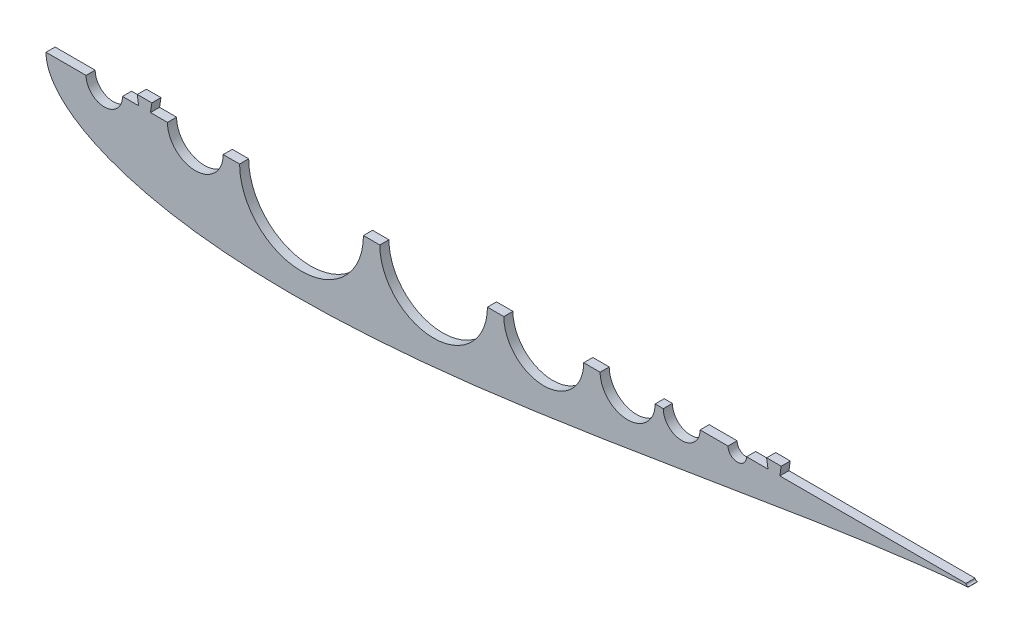
SolidWorks part; units mm, degrees
ref_plane "Front Plane" through (0, 0, 0) normal (0, 0, 1) x (1, 0, 0)
ref_plane "Top Plane" through (0, 0, 0) normal (0, 1, 0) x (1, 0, 0)
ref_plane "Right Plane" through (0, 0, 0) normal (1, 0, 0) x (0, 0, -1)
curve "Curve4"
  spline degree 3 poles (100, 0, 0) (99.8498, 0.0023, 0) (99.4759, 0.008, 0) (99.1023, 0.0238, 0) (98.8789, 0.0332, 0) knots 0 0 0 0 0.401829 1 1 1 1
curve "Curve5"
  spline degree 3 poles (99.3714, -0.0082, 0) (100.2526, 0, 0) (99.3714, 0.0082, 0) (98.8504, 0.035, 0) (97.904, 0.0811, 0) (96.8285, 0.1543, 0) (95.5159, 0.2583, 0) (94.013, 0.3972, 0) (92.313, 0.574, 0) (90.4281, 0.791, 0) (88.3655, 1.0495, 0) (86.1348, 1.3497, 0) (83.7456, 1.691, 0) (81.2082, 2.0715, 0) (78.5335, 2.4886, 0) (75.7326, 2.9386, 0) (72.8172, 3.4168, 0) (69.799, 3.9177, 0) (66.6904, 4.435, 0) (63.5039, 4.9616, 0) (60.2521, 5.4899, 0) (56.948, 6.0119, 0) (53.6049, 6.519, 0) (50.2363, 7.0024, 0) (46.8558, 7.4534, 0) (43.4774, 7.8632, 0) (40.1152, 8.2232, 0) (36.7837, 8.5249, 0) (33.4975, 8.7606, 0) (30.2716, 8.923, 0) (27.1211, 9.0055, 0) (24.0614, 9.0025, 0) (21.108, 8.909, 0) (18.277, 8.7213, 0) (15.5843, 8.4369, 0) (13.0466, 8.0543, 0) (10.6806, 7.5735, 0) (8.5039, 6.996, 0) (6.5349, 6.3253, 0) (4.7933, 5.5673, 0) (3.3001, 4.7321, 0) (2.0777, 3.8366, 0) (1.1467, 2.91, 0) (0.5165, 2.0014, 0) (0.165, 1.1816, 0) (0.0231, 0.524, 0) (-0.0093, 0, 0) (0.0231, -0.524, 0) (0.165, -1.1816, 0) (0.5165, -2.0014, 0) (1.1467, -2.91, 0) (2.0777, -3.8366, 0) (3.3001, -4.7321, 0) (4.7933, -5.5673, 0) (6.5349, -6.3253, 0) (8.5039, -6.996, 0) (10.6806, -7.5735, 0) (13.0466, -8.0543, 0) (15.5843, -8.4369, 0) (18.277, -8.7213, 0) (21.108, -8.909, 0) (24.0614, -9.0025, 0) (27.1211, -9.0055, 0) (30.2716, -8.923, 0) (33.4975, -8.7606, 0) (36.7837, -8.5249, 0) (40.1152, -8.2232, 0) (43.4774, -7.8632, 0) (46.8558, -7.4534, 0) (50.2363, -7.0024, 0) (53.6049, -6.519, 0) (56.948, -6.0119, 0) (60.2521, -5.4899, 0) (63.5039, -4.9616, 0) (66.6904, -4.435, 0) (69.799, -3.9177, 0) (72.8172, -3.4168, 0) (75.7326, -2.9386, 0) (78.5335, -2.4886, 0) (81.2082, -2.0715, 0) (83.7456, -1.691, 0) (86.1348, -1.3497, 0) (88.3655, -1.0495, 0) (90.4281, -0.791, 0) (92.313, -0.574, 0) (94.013, -0.3972, 0) (95.5159, -0.2583, 0) (96.8285, -0.1543, 0) (97.904, -0.0811, 0) (98.8504, -0.035, 0) (99.3714, -0.0082, 0) (100.2526, 0, 0) (99.3714, 0.0082, 0) knots -0.009667 -0.005395 -0.002168 0 0.002168 0.005395 0.009667 0.014967 0.021271 0.028553 0.036781 0.04592 0.055932 0.066773 0.078397 0.090755 0.103793 0.117456 0.131686 0.146422 0.1616 0.177156 0.193024 0.209135 0.225421 0.241812 0.258238 0.274629 0.290914 0.307025 0.322893 0.338448 0.353626 0.368361 0.38259 0.396253 0.40929 0.421647 0.43327 0.444109 0.454119 0.463255 0.471479 0.478755 0.485052 0.490344 0.49461 0.497833 0.5 0.502167 0.50539 0.509656 0.514948 0.521245 0.528521 0.536745 0.545881 0.555891 0.56673 0.578353 0.59071 0.603747 0.61741 0.631639 0.646374 0.661552 0.677107 0.692975 0.709086 0.725371 0.741762 0.758188 0.774579 0.790865 0.806976 0.822844 0.8384 0.853578 0.868314 0.882544 0.896207 0.909245 0.921603 0.933227 0.944068 0.95408 0.963219 0.971447 0.978729 0.985033 0.990333 0.994605 0.997832 1 1.002168 1.005395 1.009667 periodic
sketch "Sketch2" plane through (0, 0, 0) normal (0, 0, 1) x (1, 0, 0)
  line L0 (100, 0) -> (0, 0) construction
  line L1 (1.2169, -991.9959) -> (1.2169, 49008.0041) construction
  line L2 (84.709, 0) -> (123.571, 0) construction
  line L3 (125.634, 0) -> (131.6629, 0) construction
  line L4 (643.5991, 0) -> (643.5991, -1.016)
  line L9 (0, 0) -> (643.9668, 0)
  line L13 (460.661, 0) -> (473.361, 0)
  circle A0 centre (104.14, 0) radius 19.431 construction
  arc A1 (1.2169, -4.6585) -> (1.2169, 4.6585) centre (9.525, 0) cw
  arc A2 (641.5671, 0) -> (644.1071, 0) centre (642.8371, 0) ccw
  circle A4 centre (104.14, 0) radius 19.431
  circle A9 centre (40.64, 0) radius 12.7
  circle A14 centre (642.3793, 0) radius 1.5875 construction
  arc A15 (642.5108, -1.582) -> (642.5108, 1.582) centre (642.3793, 0) ccw
  spline S2 degree 3 poles (666.3448, -0.0547) (672.2538, 0) (666.3448, 0.0547) (662.8509, 0.2344) (656.505, 0.5436) (649.293, 1.0348) (640.4916, 1.7319) (630.4138, 2.6634) (619.0141, 3.8493) (606.375, 5.3044) (592.5439, 7.0376) (577.5855, 9.0506) (561.5643, 11.3389) (544.5497, 13.8907) (526.6141, 16.6877) (507.8326, 19.7051) (488.2827, 22.9117) (468.0444, 26.2704) (447.1994, 29.739) (425.8316, 33.2703) (404.0263, 36.8132) (381.8707, 40.3133) (359.4533, 43.7135) (336.8645, 46.9554) (314.1962, 49.9798) (291.5418, 52.7277) (268.9963, 55.1412) (246.6566, 57.1646) (224.6209, 58.7452) (202.9892, 59.8341) (181.8631, 60.3875) (161.3458, 60.367) (141.542, 59.7399) (122.5581, 58.4818) (104.5023, 56.5743) (87.485, 54.0089) (71.6197, 50.7848) (57.0237, 46.9125) (43.8205, 42.415) (32.1416, 37.3322) (22.1291, 31.7315) (13.9324, 25.7264) (7.6896, 19.5132) (3.4631, 13.4204) (1.1063, 7.9234) (0.1546, 3.5138) (-0.0622, 0) (0.1546, -3.5138) (1.1063, -7.9234) (3.4631, -13.4204) (7.6896, -19.5132) (13.9324, -25.7264) (22.1291, -31.7315) (32.1416, -37.3322) (43.8205, -42.415) (57.0237, -46.9125) (71.6197, -50.7848) (87.485, -54.0089) (104.5023, -56.5743) (122.5581, -58.4818) (141.542, -59.7399) (161.3458, -60.367) (181.8631, -60.3875) (202.9892, -59.8341) (224.6209, -58.7452) (246.6566, -57.1646) (268.9963, -55.1412) (291.5418, -52.7277) (314.1962, -49.9798) (336.8645, -46.9554) (359.4533, -43.7135) (381.8707, -40.3133) (404.0263, -36.8132) (425.8316, -33.2703) (447.1994, -29.739) (468.0444, -26.2704) (488.2827, -22.9117) (507.8326, -19.7051) (526.6141, -16.6877) (544.5497, -13.8907) (561.5643, -11.3389) (577.5855, -9.0506) (592.5439, -7.0376) (606.375, -5.3044) (619.0141, -3.8493) (630.4138, -2.6634) (640.4916, -1.7319) (649.293, -1.0348) (656.505, -0.5436) (662.8509, -0.2344) (666.3448, -0.0547) (672.2538, 0) (666.3448, 0.0547) knots -0.009667 -0.005395 -0.002168 0 0.002168 0.005395 0.009667 0.014967 0.021271 0.028553 0.036781 0.04592 0.055932 0.066773 0.078397 0.090755 0.103793 0.117456 0.131686 0.146422 0.1616 0.177156 0.193024 0.209135 0.225421 0.241812 0.258238 0.274629 0.290914 0.307025 0.322893 0.338448 0.353626 0.368361 0.38259 0.396253 0.40929 0.421647 0.43327 0.444109 0.454119 0.463255 0.471479 0.478755 0.485052 0.490344 0.49461 0.497833 0.5 0.502167 0.50539 0.509656 0.514948 0.521245 0.528521 0.536745 0.545881 0.555891 0.56673 0.578353 0.59071 0.603747 0.61741 0.631639 0.646374 0.661552 0.677107 0.692975 0.709086 0.725371 0.741762 0.758188 0.774579 0.790865 0.806976 0.822844 0.8384 0.853578 0.868314 0.882544 0.896207 0.909245 0.921603 0.933227 0.944068 0.95408 0.963219 0.971447 0.978729 0.985033 0.990333 0.994605 0.997832 1 1.002168 1.005395 1.009667 only from (670.56, 0) to (670.56, 0)
  point P2 (167.64, 0)
  point P8 (1.2169, -4.6585)
  point P10 (1.2169, 4.6585)
  point P25 (0, 0)
  point P26 (644.0685, 0)
  point P27 (642.873, 0)
  point P28 (133.9182, 0)
  point P29 (0, 0)
  point P49 (130.0977, 0)
  point P59 (95.1064, 0)
  dimension "D2" = 38.862
  dimension "D3" = 1.016
  dimension "D4" = 1.27
  dimension "D8" = 25.4
  dimension "D9" = 63.5
  dimension "D10" = 3.175
  dimension "D1" = 167.64
  dimension "D6" = 63.5
extrude "Boss-Extrude1" add sketch "Sketch2" along normal blind 6.35
sketch "Sketch3" plane through (0, 0, 6.35) normal (0, 0, 1) x (1, 0, 0)
  line L0 (84.14, -12.7) -> (62.637, -12.7) construction
  line L1 (430.4749, -1041.2705) -> (430.4749, 48958.7295) construction
  line L2 (123.571, 0) -> (641.5671, 0) construction
  line L3 (27.94, 0) -> (0, 0)
  line L4 (641.5671, 0) -> (123.571, 0)
  line L5 (84.709, 0) -> (53.34, 0)
  line L6 (27.94, 0) -> (0, 0)
  line L7 (221.3683, -1000) -> (221.3683, 49000) construction
  line L8 (84.709, 0) -> (53.34, 0)
  line L9 (232.7983, -1000) -> (232.7983, 49000) construction
  line L10 (307.8396, -1000) -> (307.8396, 49000) construction
  line L11 (319.2696, -1000) -> (319.2696, 49000) construction
  line L12 (374.9948, -1000) -> (374.9948, 49000) construction
  line L13 (84.709, -17.145) -> (65.0689, -17.145) construction
  line L14 (424.7788, -1000) -> (424.7788, 49000) construction
  line L15 (135.001, -1000) -> (135.001, 49000) construction
  line L16 (386.4248, -1000) -> (386.4248, 49000) construction
  line L17 (52.7726, -27.2676) -> (52.7726, -27.2676) construction
  arc A0 (36.4352, -25.0495) -> (62.637, -12.7) centre (40.64, 0) ccw construction
  circle A2 centre (178.1847, 0) radius 43.1837
  arc A3 (642.5108, -1.582) -> (643.5991, -1.016) centre (642.3793, 0) ccw
  arc A4 (84.709, 0) -> (123.571, 0) centre (104.14, 0) ccw
  arc A5 (27.94, 0) -> (53.34, 0) centre (40.64, 0) ccw
  arc A6 (642.5108, -1.582) -> (643.5991, -1.016) centre (642.3793, 0) ccw
  circle A7 centre (270.319, 0) radius 37.5206
  arc A8 (27.94, 0) -> (53.34, 0) centre (40.64, 0) ccw
  circle A9 centre (347.1322, 0) radius 27.8626
  circle A10 centre (405.6018, 0) radius 19.177
  circle A11 centre (443.3019, 0) radius 12.827
  circle A12 centre (482.0825, 0) radius 6.477
  arc A13 (52.7726, -27.2676) -> (65.0689, -17.145) centre (40.64, 0) ccw construction
  arc A14 (638.2053, 15.2585) -> (638.2053, 15.2585) centre (638.2053, 15.2585) ccw construction
  arc A18 (641.5671, 0) -> (643.5991, -1.016) centre (642.8371, 0) ccw
  arc A19 (641.5671, 0) -> (643.5991, -1.016) centre (642.8371, 0) ccw
  spline S1 degree 3 poles (1083.539, -1665.6175) (237.9838, 156.2926) (-13.4194, 59.3783) (1.1063, -7.9234) (3.4631, -13.4204) (7.6896, -19.5132) (13.9324, -25.7264) (22.1291, -31.7315) (32.1416, -37.3322) (43.8205, -42.415) (57.0237, -46.9125) (71.6197, -50.7848) (87.485, -54.0089) (104.5023, -56.5743) (122.5581, -58.4818) (141.542, -59.7399) (161.3458, -60.367) (181.8631, -60.3875) (202.9892, -59.8341) (224.6209, -58.7452) (246.6566, -57.1646) (268.9963, -55.1412) (291.5418, -52.7277) (314.1962, -49.9798) (336.8645, -46.9554) (359.4533, -43.7135) (381.8707, -40.3133) (404.0263, -36.8132) (425.8316, -33.2703) (447.1994, -29.739) (468.0444, -26.2704) (488.2827, -22.9117) (507.8326, -19.7051) (526.6141, -16.6877) (544.5497, -13.8907) (561.5643, -11.3389) (577.5855, -9.0506) (592.5439, -7.0376) (606.375, -5.3044) (619.0141, -3.8493) (630.4138, -2.6634) (741.1247, 7.5694) (864.0226, -5.3554) (-1347.5502, -198.2161) knots 0.362281 0.362281 0.362281 0.362281 0.502167 0.50539 0.509656 0.514948 0.521245 0.528521 0.536745 0.545881 0.555891 0.56673 0.578353 0.59071 0.603747 0.61741 0.631639 0.646374 0.661552 0.677107 0.692975 0.709086 0.725371 0.741762 0.758188 0.774579 0.790865 0.806976 0.822844 0.8384 0.853578 0.868314 0.882544 0.896207 0.909245 0.921603 0.933227 0.944068 0.95408 0.963219 0.971447 0.978729 1.20286 1.20286 1.20286 1.20286 only from (0, 0) to (642.5108, -1.582)
  spline S2 degree 3 poles (0, 0) (0, -1.0075) (0.1546, -3.5138) (1.1063, -7.9234) (3.4631, -13.4204) (7.6896, -19.5132) (13.9324, -25.7264) (22.1291, -31.7315) (32.1416, -37.3322) (43.8205, -42.415) (57.0237, -46.9125) (71.6197, -50.7848) (87.485, -54.0089) (104.5023, -56.5743) (122.5581, -58.4818) (141.542, -59.7399) (161.3458, -60.367) (181.8631, -60.3875) (202.9892, -59.8341) (224.6209, -58.7452) (246.6566, -57.1646) (268.9963, -55.1412) (291.5418, -52.7277) (314.1962, -49.9798) (336.8645, -46.9554) (359.4533, -43.7135) (381.8707, -40.3133) (404.0263, -36.8132) (425.8316, -33.2703) (447.1994, -29.739) (468.0444, -26.2704) (488.2827, -22.9117) (507.8326, -19.7051) (526.6141, -16.6877) (544.5497, -13.8907) (561.5643, -11.3389) (577.5855, -9.0506) (592.5439, -7.0376) (606.375, -5.3044) (619.0141, -3.8493) (630.4138, -2.6634) (638.0937, -1.9535) (641.9934, -1.6251) (642.5108, -1.582) knots 0.5 0.5 0.5 0.5 0.502167 0.50539 0.509656 0.514948 0.521245 0.528521 0.536745 0.545881 0.555891 0.56673 0.578353 0.59071 0.603747 0.61741 0.631639 0.646374 0.661552 0.677107 0.692975 0.709086 0.725371 0.741762 0.758188 0.774579 0.790865 0.806976 0.822844 0.8384 0.853578 0.868314 0.882544 0.896207 0.909245 0.921603 0.933227 0.944068 0.95408 0.963219 0.971447 0.978729 0.979843 0.979843 0.979843 0.979843
  spline S4 degree 1 poles (52.7726, -27.2676) (638.2053, 15.2585) knots 0 0 1 1 construction
  spline S5 degree 3 poles (52.7726, -27.2676) (54.098, -27.7509) (56.7529, -28.6784) (62.1794, -30.4243) (69.1006, -32.3953) (77.5892, -34.4571) (89.0862, -36.8389) (103.7331, -39.1926) (127.5352, -41.8455) (149.5112, -42.9751) (171.6139, -43.2629) (184.6425, -43.1469) (205.1644, -42.6052) (230.9293, -41.2613) (259.7939, -38.828) (285.4834, -36.1555) (308.0659, -33.4851) (336.7822, -29.6913) (372.3922, -24.4911) (406.8647, -19.0063) (435.2357, -14.3425) (451.6826, -11.6119) (464.2574, -9.5208) (476.8398, -7.4307) (497.3171, -4.0443) (526.9629, 0.7645) (562.929, 6.2684) (594.1055, 10.5252) (616.0859, 13.0867) (628.694, 14.3901) (635.0364, 14.9826) (638.2053, 15.2585) knots 0.548481 0.548481 0.548481 0.548481 0.551835 0.555189 0.561898 0.568606 0.575315 0.588731 0.602148 0.628982 0.637543 0.65096 0.657668 0.682649 0.707463 0.72088 0.738887 0.756894 0.783728 0.816817 0.832298 0.845715 0.852722 0.859728 0.873145 0.897318 0.924152 0.950985 0.964402 0.971111 0.977819 0.977819 0.977819 0.977819 construction
  line M19 (641.5671, 0) -> (123.571, 0)
  dimension "D3" = 11.43
  dimension "D7" = 38.354
  dimension "D8" = 25.654
  dimension "D9" = 12.954
  dimension "D4" = 11.43
  dimension "D5" = 11.43
  dimension "D6" = 11.43
  dimension "D1" = 0
  dimension "D10" = 17.145
extrude "Cut-Extrude2" cut sketch "Sketch3" against normal through all both and the other way through all contours A2 M19 | A7 M19 | A9 M19 | A10 M19 | A11 M19 | A12 M19
sketch "Sketch4" plane through (0, 0, 6.35) normal (0, 0, 1) x (1, 0, 0)
  line L0 (63.66, 6.35) -> (73.82, 6.35)
  line L1 (65.565, 6.35) -> (71.915, 6.35)
  line L2 (65.565, 6.35) -> (65.565, -6.35)
  line L3 (65.565, -6.35) -> (71.915, -6.35)
  line L4 (71.915, 6.35) -> (71.915, -6.35)
  line L5 (65.565, 6.35) -> (71.915, -6.35) construction
  line L6 (65.565, -6.35) -> (71.915, 6.35) construction
  line L7 (71.915, -6.35) -> (73.82, 6.35)
  line L8 (63.66, 6.35) -> (65.565, -6.35)
  line L9 (232.7983, 0) -> (221.3683, 0)
  line L18 (232.7983, 0) -> (221.3683, 0)
  line L20 (135.001, 0) -> (123.571, 0)
  line L21 (135.001, 0) -> (123.571, 0)
  line L22 (84.709, 0) -> (53.34, 0)
  line L23 (84.709, 0) -> (53.34, 0)
  line L24 (27.94, 0) -> (0, 0)
  line L25 (27.94, 0) -> (0, 0)
  line L26 (641.5671, 0) -> (488.5595, 0)
  line L27 (502.5295, 6.35) -> (512.6895, 6.35)
  line L28 (504.4345, 6.35) -> (510.7845, 6.35)
  line L29 (504.4345, 6.35) -> (504.4345, -6.35)
  line L30 (504.4345, -6.35) -> (510.7845, -6.35)
  line L31 (510.7845, 6.35) -> (510.7845, -6.35)
  line L32 (504.4345, 6.35) -> (510.7845, -6.35) construction
  line L33 (504.4345, -6.35) -> (510.7845, 6.35) construction
  line L34 (504.4345, -6.35) -> (502.5295, 6.35)
  line L35 (510.7845, -6.35) -> (512.6895, 6.35)
  line L36 (641.5671, 0) -> (488.5595, 0)
  line L37 (475.6055, 0) -> (456.1289, 0)
  line L38 (475.6055, 0) -> (456.1289, 0)
  line L39 (430.4749, 0) -> (424.7788, 0)
  line L40 (430.4749, 0) -> (424.7788, 0)
  line L41 (386.4248, 0) -> (374.9948, 0)
  line L42 (386.4248, 0) -> (374.9948, 0)
  line L43 (319.2696, 0) -> (307.8396, 0)
  line L44 (319.2696, 0) -> (307.8396, 0)
  arc A9 (232.7983, 0) -> (307.8396, 0) centre (270.319, 0) ccw
  arc A10 (232.7983, 0) -> (307.8396, 0) centre (270.319, 0) ccw
  arc A11 (135.001, 0) -> (221.3683, 0) centre (178.1847, 0) ccw
  arc A12 (135.001, 0) -> (221.3683, 0) centre (178.1847, 0) ccw
  arc A13 (84.709, 0) -> (123.571, 0) centre (104.14, 0) ccw
  arc A14 (84.709, 0) -> (123.571, 0) centre (104.14, 0) ccw
  arc A15 (27.94, 0) -> (53.34, 0) centre (40.64, 0) ccw
  arc A16 (386.4248, 0) -> (424.7788, 0) centre (405.6018, 0) ccw
  arc A17 (27.94, 0) -> (53.34, 0) centre (40.64, 0) ccw
  arc A18 (642.5108, -1.582) -> (643.5991, -1.016) centre (642.3793, 0) ccw
  arc A19 (642.5108, -1.582) -> (643.5991, -1.016) centre (642.3793, 0) ccw
  arc A20 (475.6055, 0) -> (488.5595, 0) centre (482.0825, 0) ccw
  arc A21 (475.6055, 0) -> (488.5595, 0) centre (482.0825, 0) ccw
  arc A22 (430.4749, 0) -> (456.1289, 0) centre (443.3019, 0) ccw
  arc A23 (430.4749, 0) -> (456.1289, 0) centre (443.3019, 0) ccw
  arc A24 (319.2696, 0) -> (374.9948, 0) centre (347.1322, 0) ccw
  arc A25 (386.4248, 0) -> (424.7788, 0) centre (405.6018, 0) ccw
  arc A26 (319.2696, 0) -> (374.9948, 0) centre (347.1322, 0) ccw
  arc A28 (641.5671, 0) -> (643.5991, -1.016) centre (642.8371, 0) ccw
  arc A29 (641.5671, 0) -> (643.5991, -1.016) centre (642.8371, 0) ccw
  spline S1 degree 3 poles (1083.539, -1665.6175) (237.9838, 156.2926) (-13.4194, 59.3783) (1.1063, -7.9234) (3.4631, -13.4204) (7.6896, -19.5132) (13.9324, -25.7264) (22.1291, -31.7315) (32.1416, -37.3322) (43.8205, -42.415) (57.0237, -46.9125) (71.6197, -50.7848) (87.485, -54.0089) (104.5023, -56.5743) (122.5581, -58.4818) (141.542, -59.7399) (161.3458, -60.367) (181.8631, -60.3875) (202.9892, -59.8341) (224.6209, -58.7452) (246.6566, -57.1646) (268.9963, -55.1412) (291.5418, -52.7277) (314.1962, -49.9798) (336.8645, -46.9554) (359.4533, -43.7135) (381.8707, -40.3133) (404.0263, -36.8132) (425.8316, -33.2703) (447.1994, -29.739) (468.0444, -26.2704) (488.2827, -22.9117) (507.8326, -19.7051) (526.6141, -16.6877) (544.5497, -13.8907) (561.5643, -11.3389) (577.5855, -9.0506) (592.5439, -7.0376) (606.375, -5.3044) (619.0141, -3.8493) (630.4138, -2.6634) (741.1247, 7.5694) (864.0226, -5.3554) (-1347.5502, -198.2161) knots 0.362281 0.362281 0.362281 0.362281 0.502167 0.50539 0.509656 0.514948 0.521245 0.528521 0.536745 0.545881 0.555891 0.56673 0.578353 0.59071 0.603747 0.61741 0.631639 0.646374 0.661552 0.677107 0.692975 0.709086 0.725371 0.741762 0.758188 0.774579 0.790865 0.806976 0.822844 0.8384 0.853578 0.868314 0.882544 0.896207 0.909245 0.921603 0.933227 0.944068 0.95408 0.963219 0.971447 0.978729 1.20286 1.20286 1.20286 1.20286 only from (0, 0) to (642.5108, -1.582)
  spline S2 degree 3 poles (0, 0) (0, -1.0075) (0.1546, -3.5138) (1.1063, -7.9234) (3.4631, -13.4204) (7.6896, -19.5132) (13.9324, -25.7264) (22.1291, -31.7315) (32.1416, -37.3322) (43.8205, -42.415) (57.0237, -46.9125) (71.6197, -50.7848) (87.485, -54.0089) (104.5023, -56.5743) (122.5581, -58.4818) (141.542, -59.7399) (161.3458, -60.367) (181.8631, -60.3875) (202.9892, -59.8341) (224.6209, -58.7452) (246.6566, -57.1646) (268.9963, -55.1412) (291.5418, -52.7277) (314.1962, -49.9798) (336.8645, -46.9554) (359.4533, -43.7135) (381.8707, -40.3133) (404.0263, -36.8132) (425.8316, -33.2703) (447.1994, -29.739) (468.0444, -26.2704) (488.2827, -22.9117) (507.8326, -19.7051) (526.6141, -16.6877) (544.5497, -13.8907) (561.5643, -11.3389) (577.5855, -9.0506) (592.5439, -7.0376) (606.375, -5.3044) (619.0141, -3.8493) (630.4138, -2.6634) (638.0937, -1.9535) (641.9934, -1.6251) (642.5108, -1.582) knots 0.5 0.5 0.5 0.5 0.502167 0.50539 0.509656 0.514948 0.521245 0.528521 0.536745 0.545881 0.555891 0.56673 0.578353 0.59071 0.603747 0.61741 0.631639 0.646374 0.661552 0.677107 0.692975 0.709086 0.725371 0.741762 0.758188 0.774579 0.790865 0.806976 0.822844 0.8384 0.853578 0.868314 0.882544 0.896207 0.909245 0.921603 0.933227 0.944068 0.95408 0.963219 0.971447 0.978729 0.979843 0.979843 0.979843 0.979843
  point P0 (68.74, 0)
  point P15 (68.74, 6.35)
  point P25 (68.74, 6.35)
  point P37 (507.6095, 0)
  point P44 (507.6095, 6.35)
  point P45 (507.6095, 6.35)
  line M32 (84.709, 0) -> (53.34, 0)
  dimension "D2" = 6.35
  dimension "D3" = 10.16
  dimension "D4" = 12.7
  dimension "D5" = 6.35
  dimension "D6" = 12.7
  dimension "D7" = 19.05
  dimension "D8" = 10.16
  dimension "D1" = 0
extrude "Boss-Extrude2" add sketch "Sketch4" against normal up to surface (6.35 mm away) contours L34 L36 L29 L27 | L31 L27 L29 L36 | L36 L35 L27 L31 | L0 L8 L2 M32 | L4 L0 L2 M32 | L7 L0 L4 M32 up to face at (307.4484, -9.0862, 0)
equation "\"0.5n\"=0"
